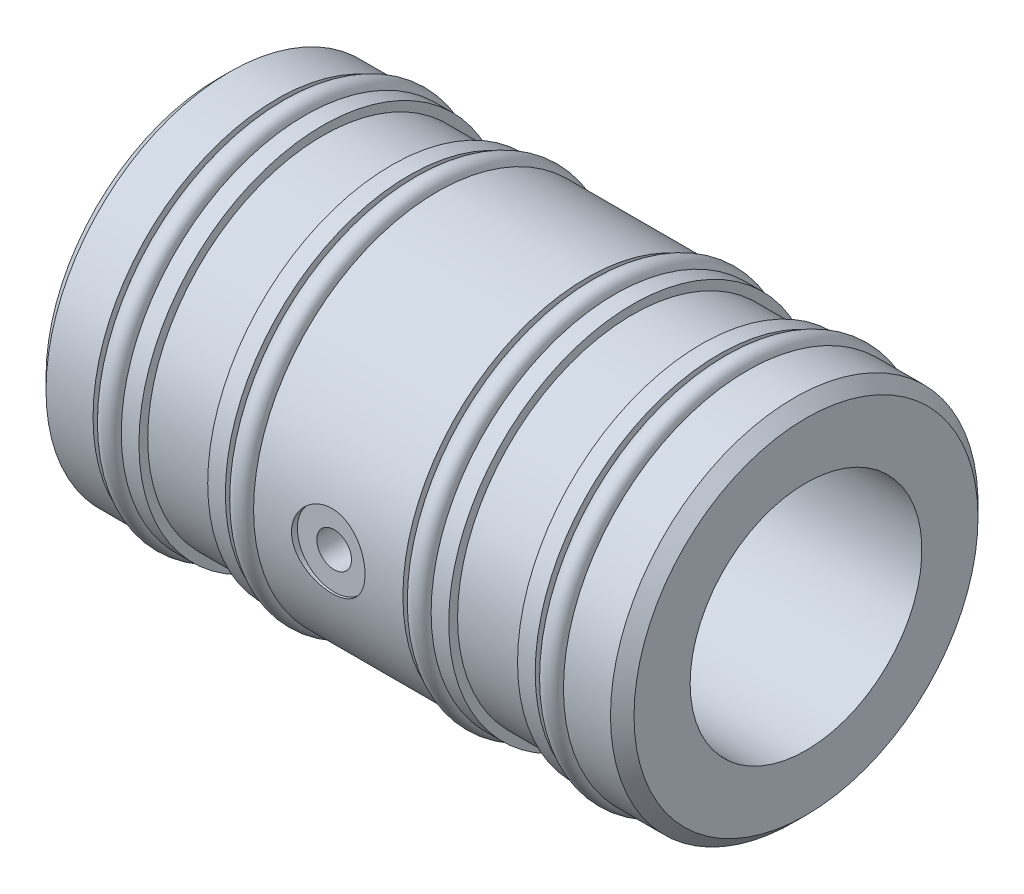
SolidWorks part; units mm, degrees
ref_plane "Front Plane" through (0, 0, 0) normal (0, 0, 1) x (1, 0, 0)
ref_plane "Top Plane" through (0, 0, 0) normal (0, 1, 0) x (1, 0, 0)
ref_plane "Right Plane" through (0, 0, 0) normal (1, 0, 0) x (0, 0, -1)
sketch "Sketch1" plane through (0, 0, 0) normal (0, 0, 1) x (1, 0, 0)
  line L0 (0, 10.01) -> (50.8, 10.01)
  line L1 (50.8, 10.01) -> (50.8, 15.875)
  line L2 (50.8, 15.875) -> (45.718, 15.875)
  line L3 (45.718, 15.875) -> (45.718, 14.605)
  line L4 (45.718, 14.605) -> (43.28, 14.605)
  line L5 (43.28, 14.605) -> (43.28, 15.875)
  line L6 (43.28, 15.875) -> (41.754, 15.875)
  line L7 (41.754, 15.875) -> (41.754, 15.113)
  line L8 (0, 10.01) -> (0, 15.875)
  line L9 (0, 15.875) -> (5.08, 15.875)
  line L10 (5.08, 15.875) -> (5.08, 14.605)
  line L11 (5.08, 14.605) -> (7.518, 14.605)
  line L12 (7.518, 14.605) -> (7.518, 15.875)
  line L13 (7.518, 15.875) -> (9.042, 15.875)
  line L14 (9.042, 15.875) -> (9.042, 15.113)
  line L15 (9.042, 15.113) -> (14.986, 15.113)
  line L16 (14.986, 15.113) -> (14.986, 15.875)
  line L17 (14.986, 15.875) -> (16.51, 15.875)
  line L18 (16.51, 15.875) -> (16.51, 14.605)
  line L19 (16.51, 14.605) -> (18.948, 14.605)
  line L20 (18.948, 14.605) -> (18.948, 15.875)
  line L21 (18.948, 15.875) -> (31.85, 15.875)
  line L22 (31.85, 15.875) -> (31.85, 14.605)
  line L23 (41.754, 15.113) -> (35.81, 15.113)
  line L24 (35.81, 15.113) -> (35.81, 15.875)
  line L25 (35.81, 15.875) -> (34.288, 15.875)
  line L26 (34.288, 15.875) -> (34.288, 14.605)
  line L27 (34.288, 14.605) -> (31.85, 14.605)
  line L28 (0, 0) -> (50.8, 0) construction
  dimension "Bore ID" = 20.02
  dimension "OAL" = 50.8
  dimension "Moglice groove width" = 5.944
  dimension "O-ring groove width" = 2.438
  dimension "Edge to 1st o-ring groove" = 5.08
  dimension "Edge to 2nd o-ring groove" = 16.51
  dimension "Bushing OD" = 31.75
  dimension "O-ring groove dia" = 29.21
  dimension "Edge to 3rd o-ring groove" = 31.85
  dimension "edge to 4th o-ring groove" = 43.28
  dimension "Edge to 1st moglice groove" = 9.042
  dimension "Edge to 2nd moglice groove" = 35.81
  dimension "Moglice Groove Dia" = 30.226
revolve "Revolve1" add sketch "Sketch1" angle 360 about L28
chamfer "Chamfer1" distance 1.016 angle 45 2 edges at (0, 0, 15.875) (50.8, 0, 15.875)
ref_plane "Plane1" through (0, 0, -7.9121) normal (0, 0, 1) x (1, 0, 0)
hole_wizard "3/8 (0.375) Diameter Hole1" positions "3DSketch1" profile "Sketch2" hole size "3/8" standard "Ansi Inch"
sketch3d "3DSketch1"
  point P0 (25.4, 0, 15.875)
  dimension "Edge to air hole" = 25.4
sketch "Sketch2" plane through (25.4, 0, 15.875) normal (1, 0, 0) x (0, -1, 0)
  line L0 (0, 0) -> (0, 0.508)
  line L1 (0, 0.508) -> (3.175, 0.508)
  line L2 (3.175, 0.508) -> (3.175, 0)
  line L5 (3.175, 0) -> (0, 0)
  line L10 (0, 0.508) -> (-3.175, 0.508) construction
  line L11 (0, -6.35) -> (0, 107.95) construction
  dimension "Hole Dia." = 6.35
  dimension "Hole Depth" = 0.508
  dimension "Drill Angle" = 180
hole_wizard "Air Hole" positions "Sketch4" profile "Sketch3" tap size "M3x0.5" standard "Ansi Metric"
sketch "Sketch4" plane through (0, 0, 15.367) normal (0, 0, 1) x (1, 0, 0)
  circle A0 centre (25.4, 0) radius 3.175 construction
  point P0 (25.4, 0)
sketch "Sketch3" plane through (25.4, 0, 15.367) normal (1, 0, 0) x (0, -1, 0)
  line L0 (0, 0) -> (0, 7.0978)
  line L1 (0, 7.0978) -> (1.2446, 6.35)
  line L2 (1.2446, 6.35) -> (1.2446, 5.994)
  line L3 (1.2446, 5.994) -> (1.4985, 5.994)
  line L4 (1.4985, 5.994) -> (1.4985, 0)
  line L5 (1.4985, 0) -> (0, 0)
  line L10 (0, 7.0978) -> (-1.2446, 6.35) construction
  line L11 (0, -6.35) -> (0, 107.95) construction
  dimension "Tap Drill Dia." = 2.4892
  dimension "Tap Drill Depth" = 6.35
  dimension "Thread Major Dia." = 2.997
  dimension "Thread Depth" = 5.994
  dimension "Drill Angle" = 118
sketch "Sketch5" plane through (0, 0, 0) normal (0, 0, 1) x (1, 0, 0)
  line L3 (7.518, 15.875) -> (7.518, -15.875) construction
  line L4 (18.948, 15.875) -> (18.948, -15.875) construction
  line L5 (31.85, -15.875) -> (31.85, 15.875) construction
  line L6 (43.28, -15.875) -> (43.28, 15.875) construction
  line L7 (0, 0) -> (51.7691, 0) construction
  circle A0 centre (44.5, 15.4788) radius 0.8763
  circle A1 centre (33.07, 15.4788) radius 0.8763
  circle A2 centre (17.728, 15.4788) radius 0.8763
  circle A3 centre (6.2988, 15.4788) radius 0.8763
  dimension "D1" = 1.7526
  dimension "D2" = 16.3551
  dimension "D6" = 1.22
  dimension "D3" = 1.2192
  dimension "D4" = 1.22
  dimension "D5" = 1.22
revolve "Revolve2" add sketch "Sketch5" angle 360 about L7
equation "\"plane offset\"= \"Bushing OD@Sketch1\" / 2"
